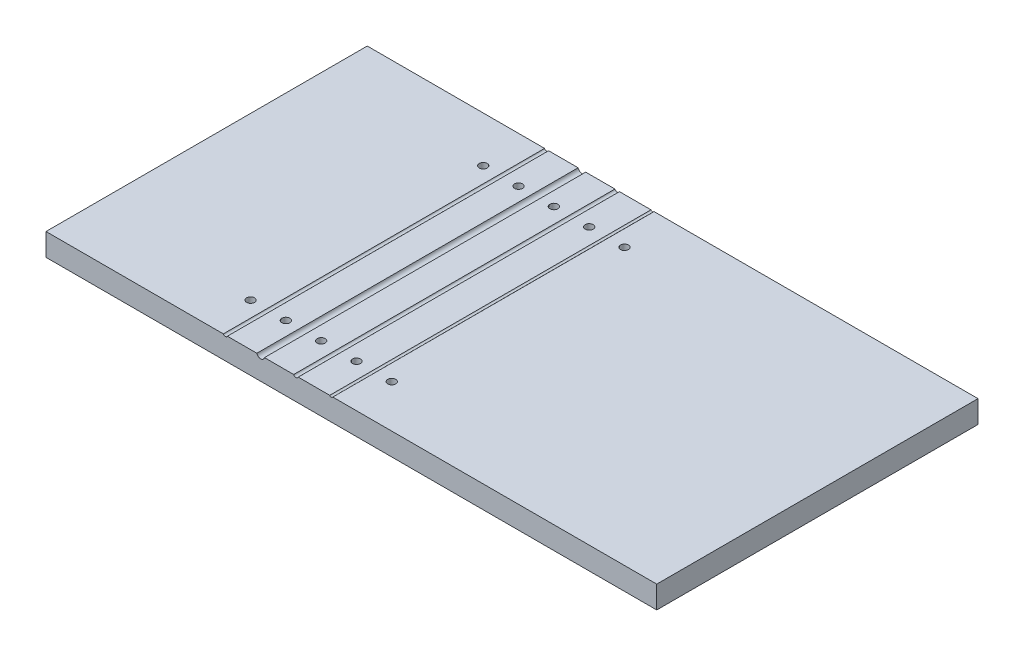
SolidWorks part; units mm, degrees
ref_plane "Front Plane" through (0, 0, 0) normal (0, 0, 1) x (1, 0, 0)
ref_plane "Top Plane" through (0, 0, 0) normal (0, 1, 0) x (1, 0, 0)
ref_plane "Right Plane" through (0, 0, 0) normal (1, 0, 0) x (0, 0, -1)
sketch "Sketch1" plane through (0, 0, 0) normal (0, 1, 0) x (1, 0, 0)
  line L1 (-6.3794, 85.4337) -> (166.6206, 85.4337)
  line L2 (-6.3794, 85.4337) -> (-6.3794, -5.5663)
  line L3 (-6.3794, -5.5663) -> (166.6206, -5.5663)
  line L4 (166.6206, 85.4337) -> (166.6206, -5.5663)
  dimension "D1" = 91
  dimension "D2" = 173
extrude "Boss-Extrude1" add sketch "Sketch1" along normal blind 6.35
sketch "Sketch2" plane through (0, 0, 5.5663) normal (0, 0, 1) x (1, 0, 0)
  line L0 (54.4206, 6.6) -> (81.4623, 6.6) construction
  line L3 (44.4206, 6.6) -> (54.4206, 6.6) construction
  line L4 (-6.3794, 6.35) -> (166.6206, 6.35) construction
  circle A0 centre (44.4206, 6.6) radius 0.6223
  circle A1 centre (54.4206, 6.6) radius 1.1
  circle A2 centre (64.4206, 6.6) radius 0.6858
  circle A3 centre (74.4206, 6.6) radius 0.5
  dimension "D1" = 1.2446
  dimension "D3" = 2.2
  dimension "D6" = 1.3716
  dimension "D7" = 1
  dimension "D2" = 0.25
  dimension "D4" = 10
  dimension "D5" = 50.8
  dimension "D8" = 10
  dimension "D9" = 10
extrude "Cut-Extrude1" cut sketch "Sketch2" against normal through all
sketch "Sketch3" plane through (0, 6.35, 0) normal (0, 1, 0) x (1, 0, 0)
  line L0 (49.4206, 72.4912) -> (49.4206, 6.5743) construction
  line L1 (39.4206, 72.4912) -> (59.4206, 72.4912) construction
  line L2 (39.4206, 72.4912) -> (39.4206, 6.5743) construction
  line L3 (39.4206, 6.5743) -> (59.4206, 6.5743) construction
  line L4 (59.4206, 72.4912) -> (59.4206, 6.5743) construction
  line L5 (44.9905, 85.4337) -> (43.8507, 85.4337) construction
  line L6 (55.4918, 85.4337) -> (53.3494, 85.4337) construction
  line L7 (44.9905, 85.4337) -> (43.8507, 85.4337) construction
  line L8 (55.4918, 85.4337) -> (53.3494, 85.4337) construction
  line L9 (44.4206, 85.4337) -> (44.4206, -5.5825) construction
  line L10 (54.4206, 85.4337) -> (54.4206, -5.5825) construction
  line L11 (59.4206, 72.4912) -> (79.4206, 72.4912) construction
  line L12 (69.4206, 72.4912) -> (69.4206, 6.5743) construction
  line L13 (59.4206, 6.5743) -> (79.4206, 6.5743) construction
  line L14 (65.0592, 85.4337) -> (63.782, 85.4337) construction
  line L15 (74.8536, 85.4337) -> (73.9876, 85.4337) construction
  line L16 (65.0592, 85.4337) -> (63.782, 85.4337) construction
  line L17 (74.8536, 85.4337) -> (73.9876, 85.4337) construction
  line L18 (64.4206, 85.4337) -> (64.4206, -5.5663) construction
  line L19 (74.4206, 85.4337) -> (74.4206, -5.5663) construction
  line L20 (79.4206, 72.4912) -> (79.4206, 6.5743) construction
  point P10 (44.4206, 85.4337)
  point P11 (54.4206, 85.4337)
  dimension "D1" = 20
  dimension "D2" = 5
  dimension "D3" = 5
  dimension "D4" = 5
hole_wizard "#4-40 Tapped Hole1" positions "Sketch5" profile "Sketch4" tap size "#4-40" standard "ANSI Inch" end condition through all
sketch "Sketch5" plane through (0, 6.35, 0) normal (0, 1, 0) x (1, 0, 0)
  point P0 (39.4206, 72.4912)
  point P3 (59.4206, 72.4912)
  point P6 (49.4206, 72.4912)
  point P9 (49.4206, 6.5743)
  point P12 (39.4206, 6.5743)
  point P15 (59.4206, 6.5743)
  point P18 (69.4206, 72.4912)
  point P21 (79.4206, 72.4912)
  point P24 (69.4206, 6.5743)
  point P27 (79.4206, 6.5743)
sketch "Sketch4" plane through (39.4206, 6.35, -72.4912) normal (1, 0, 0) x (0, 0, 1)
  line L0 (0, 0) -> (0, 6.35)
  line L1 (0, 6.35) -> (1.1303, 6.35)
  line L2 (1.1303, 6.35) -> (1.1303, 0)
  line L5 (1.1303, 0) -> (0, 0)
  line L11 (0, -6.35) -> (0, 107.95) construction
  dimension "Thru Tap Drill Dia." = 2.2606
  dimension "Thru Tap Drill Depth" = 6.35
cosmetic thread "Hole Thread1" parameters "D2"=2.8448
cosmetic thread "Hole Thread2" parameters "D2"=2.8448
cosmetic thread "Hole Thread3" parameters "D2"=2.8448
cosmetic thread "Hole Thread4" parameters "D2"=2.8448
cosmetic thread "Hole Thread5" parameters "D2"=2.8448
cosmetic thread "Hole Thread6" parameters "D2"=2.8448
cosmetic thread "Hole Thread7" parameters "D2"=2.8448
cosmetic thread "Hole Thread8" parameters "D2"=2.8448
cosmetic thread "Hole Thread9" parameters "D2"=2.8448
cosmetic thread "Hole Thread10" parameters "D2"=2.8448
